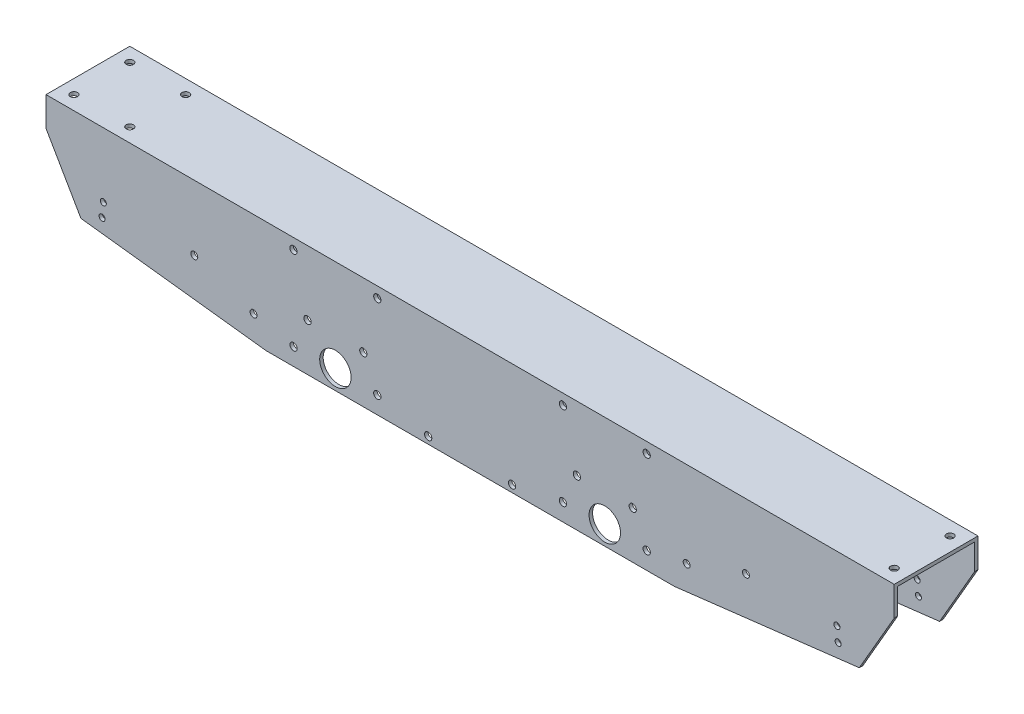
SolidWorks part; units mm, degrees
ref_plane "Front Plane" through (0, 0, 0) normal (0, 0, 1) x (1, 0, 0)
ref_plane "Top Plane" through (0, 0, 0) normal (0, 1, 0) x (1, 0, 0)
ref_plane "Right Plane" through (0, 0, 0) normal (1, 0, 0) x (0, 0, -1)
sketch "Sketch1" plane through (0, 0, 0) normal (1, 0, 0) x (0, 0, -1)
  line L0 (-34.925, 47.625) -> (-34.925, -47.625) construction
  line L1 (-38.1, 50.8) -> (38.1, 50.8)
  line L2 (-38.1, 50.8) -> (-38.1, -50.8)
  line L3 (-38.1, -50.8) -> (-34.925, -50.8)
  line L4 (38.1, 50.8) -> (38.1, -50.8)
  line L5 (-38.1, 50.8) -> (38.1, -50.8) construction
  line L6 (-38.1, -50.8) -> (38.1, 50.8) construction
  line L7 (34.925, 47.625) -> (34.925, -50.8)
  line L8 (-34.925, 47.625) -> (34.925, 47.625)
  line L9 (-34.925, 47.625) -> (-34.925, -50.8)
  line L10 (-34.925, -47.625) -> (34.925, -47.625) construction
  line L11 (34.925, 47.625) -> (34.925, -47.625) construction
  line L12 (-38.1, -50.8) -> (38.1, -50.8) construction
  line L13 (38.1, -50.8) -> (34.925, -50.8)
  point P0 (0, 0)
  dimension "D1" = 76.2
  dimension "D2" = 101.6
  dimension "D3" = 3.175
extrude "Boss-Extrude1" add sketch "Sketch1" along normal mid plane 771.4115
sketch "Sketch2" plane through (0, 0, 38.1) normal (0, 0, 1) x (1, 0, 0)
  line L0 (-405.1565, -33.274) -> (428.5144, -33.274) construction
  line L1 (385.7058, -50.8) -> (-385.7058, -50.8) construction
  line L3 (-122.5, 124.7315) -> (-122.5, -108.8261) construction
  line L4 (-122.5, 124.7315) -> (-122.5, -108.8261) construction
  line L7 (0, 107.4469) -> (0, -99.4956) construction
  line L9 (0, -41.91) -> (0, 41.91) construction
  line L13 (0, 50.8) -> (0, -55.872) construction
  line L14 (385.7058, 50.8) -> (-385.7058, 50.8) construction
  circle A0 centre (-333.5772, -7.874) radius 2.75
  circle A1 centre (334.7203, -20.574) radius 2.75
  circle A2 centre (333.5772, -7.874) radius 2.75
  circle A3 centre (84.4, -35.12) radius 3.302
  circle A4 centre (-160.6, -35.12) radius 3.302
  circle A5 centre (-160.6, 41.08) radius 3.302
  circle A6 centre (-122.5, -33.274) radius 14.2875
  circle A7 centre (-334.7203, -20.574) radius 2.75
  circle A8 centre (-84.4, 41.08) radius 3.302
  circle A9 centre (-84.4, -35.12) radius 3.302
  circle A10 centre (160.6, -35.12) radius 3.302
  circle A11 centre (84.4, 41.08) radius 3.302
  circle A12 centre (160.6, 41.08) radius 3.302
  circle A13 centre (122.5, -33.274) radius 14.2875
  point P16 (-122.5, -33.274)
  dimension "D1" = 17.526
  dimension "D2" = 212.6
  dimension "D3" = 212.6
  dimension "D4" = 122.5
  dimension "D7" = 25.4
  dimension "D8" = 12.7
  dimension "D9" = 76.2
  dimension "D10" = 76.2
  dimension "D11" = 76.2
  dimension "D12" = 6.604
  dimension "D13" = 15.68
  dimension "D14" = 38.1
extrude "Axles" cut sketch "Sketch2" against normal blind 141.732
sketch "Flanigan mounting holes" plane through (0, 0, 38.1) normal (0, 0, 1) x (1, 0, 0)
  line L0 (122.5, 79.5654) -> (122.5, -33.274) construction
  line L1 (0, 77.5082) -> (0, -84.2491) construction
  line L2 (97.1, 9.7703) -> (97.1, -58.1396) construction
  line L3 (385.7058, -50.8) -> (-385.7058, -50.8) construction
  line L4 (147.9, 11.4068) -> (147.9, -61.409) construction
  line L5 (147.9, -44.45) -> (97.1, -44.45) construction
  line L6 (0, -41.91) -> (0, 41.91) construction
  circle A0 centre (-147.9, -7.87) radius 3.3
  circle A1 centre (97.1, -7.87) radius 3.3
  circle A2 centre (-97.1, -7.87) radius 3.3
  circle A3 centre (147.9, -7.87) radius 3.3
  circle A5 centre (122.5, -33.274) radius 14.2875 construction
  point P4 (147.9, -7.87)
  point P5 (97.1, -7.87)
  point P6 (122.5, 14.36)
  dimension "D6" = 42.93
  dimension "D7" = 42.93
  dimension "D8" = 6.35
  dimension "D1" = 0
  dimension "D2" = 25.4
  dimension "D3" = 25.4
  dimension "D4" = 22.23
extrude "Flanigan mounting holes extrusion" cut sketch "Flanigan mounting holes" against normal through all
sketch "Sketch16" plane through (0, 0, 38.1) normal (0, 0, 1) x (1, 0, 0)
  line L0 (-353.9515, -30.8) -> (-185.7058, -50.8)
  line L1 (-385.7058, 50.8) -> (-385.7058, -50.8) construction
  line L2 (-385.7058, 24.2) -> (-353.9515, -30.8)
  line L3 (385.7058, -50.8) -> (-385.7058, -50.8) construction
  line L4 (-385.7058, 24.2) -> (-385.7058, -50.8)
  line L5 (-385.7058, -50.8) -> (-185.7058, -50.8)
  line L6 (0, 50.8) -> (0, -65.171) construction
  line L7 (0, -41.91) -> (0, 41.91) construction
  line L8 (0, 74.5999) -> (0, -74.6877) construction
  line L9 (385.7058, -50.8) -> (185.7058, -50.8)
  line L10 (385.7058, 24.2) -> (385.7058, -50.8)
  line L11 (385.7058, 24.2) -> (353.9515, -30.8)
  line L12 (353.9515, -30.8) -> (185.7058, -50.8)
  dimension "D1" = 60
extrude "Beveled ends" cut sketch "Sketch16" against normal blind 101.6
sketch "Sketch32" plane through (0, 0, -38.1) normal (0, 0, -1) x (-1, 0, 0)
  line L0 (0, 41.91) -> (0, -41.91) construction
  line L1 (-185.7058, -50.8) -> (185.7058, -50.8) construction
  line L3 (0, 54.6658) -> (0, -55.1985) construction
  circle A0 centre (-38.1, -44.45) radius 3.3
  circle A1 centre (38.1, -44.45) radius 3.3
  point P8 (38.1, -44.45)
  dimension "D1" = 6.6
  dimension "D3" = 6.35
  dimension "D2" = 38.1
extrude "Belt shield holes" cut sketch "Sketch32" against normal through all
sketch "Sketch37" plane through (0, 50.8, 0) normal (0, 1, 0) x (1, 0, 0)
  line L0 (385.7058, 38.1) -> (-385.7058, 38.1) construction
  line L1 (385.7058, 38.1) -> (385.7058, -38.1) construction
  line L2 (385.7058, -38.1) -> (-385.7058, -38.1) construction
  line L3 (-385.7058, 38.1) -> (-385.7058, -38.1) construction
  circle A0 centre (373.0058, 25.4) radius 3.3
  circle A1 centre (373.0058, -25.4) radius 3.3
  circle A2 centre (-322.2058, 25.4) radius 3.3
  circle A3 centre (-322.2058, -25.4) radius 3.3
  circle A4 centre (-373.0058, 25.4) radius 3.3
  circle A5 centre (-373.0058, -25.4) radius 3.3
  dimension "D1" = 6.6
  dimension "D2" = 12.7
  dimension "D3" = 12.7
  dimension "D4" = 63.5
  dimension "D6" = 12.7
  dimension "D10" = 12.7
extrude "Top holes" cut sketch "Sketch37" against normal through all
sketch "Sketch38" plane through (0, 0, 38.1) normal (0, 0, 1) x (1, 0, 0)
  line L0 (385.7058, 50.8) -> (-385.7058, 50.8) construction
  line L1 (0, 50.8) -> (0, -50.6681) construction
  line L2 (0, -41.91) -> (0, 41.91) construction
  circle A0 centre (-250.8318, -8.382) radius 3.15
  circle A1 centre (-196.9247, -27.3598) radius 3.15
  circle A2 centre (196.9247, -27.3598) radius 3.15
  circle A3 centre (250.8318, -8.382) radius 3.15
  dimension "D1" = 59.182
  dimension "D2" = 134.874
  dimension "D3" = 6.3
  dimension "D4" = 57.15
  dimension "D6" = 6.3
  dimension "D5" = 188.781
extrude "Cut-Extrude1" cut sketch "Sketch38" against normal through all
